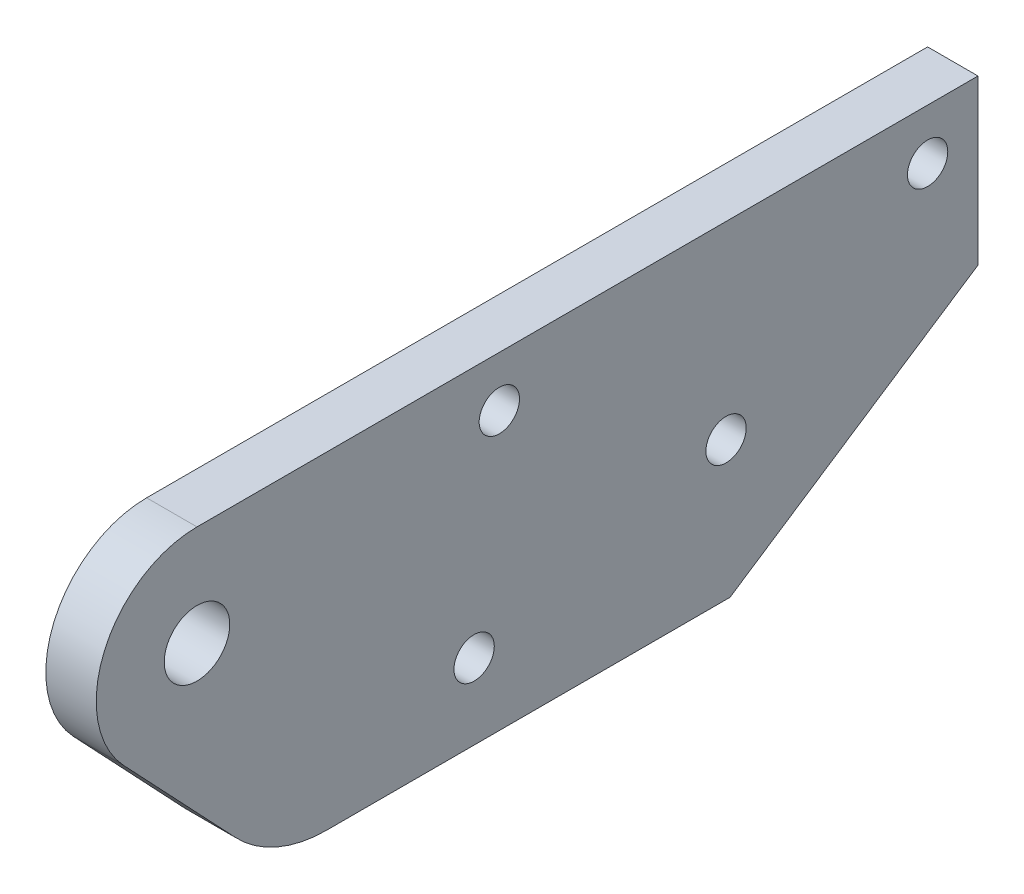
SolidWorks part; units mm, degrees
ref_plane "前视基准面" through (0, 0, 0) normal (0, 0, 1) x (1, 0, 0)
ref_plane "上视基准面" through (0, 0, 0) normal (0, 1, 0) x (1, 0, 0)
ref_plane "右视基准面" through (0, 0, 0) normal (1, 0, 0) x (0, 0, -1)
sketch "草图1" plane through (0, 0, 0) normal (1, 0, 0) x (0, 0, -1)
  line L0 (8.1049, 1.8788) -> (27.7954, 14.8788)
  line L1 (27.7954, 27.8788) -> (-34.2046, 27.8788)
  line L2 (27.7954, 27.8788) -> (27.7954, 14.8788)
  line L3 (8.1049, 1.8788) -> (-23.8951, 1.8788)
  line L10 (-31.1641, 5.0114) -> (-40.0198, 14.3849)
  circle A0 centre (23.7954, 23.8788) radius 1.6
  circle A1 centre (-10.2046, 23.8788) radius 1.6
  arc A2 (-34.2046, 27.8788) -> (-40.0198, 14.3849) centre (-34.2046, 19.8788) ccw
  circle A3 centre (7.7954, 12.8788) radius 1.6
  circle A4 centre (-12.2046, 7.8788) radius 1.6
  circle A5 centre (-34.2046, 19.8788) radius 2.6
  arc A6 (-23.8951, 1.8788) -> (-31.1641, 5.0114) centre (-23.8951, 11.8788) cw
  point P0 (-150, 0)
  point P1 (135, 0)
  point P9 (-344.9533, 138.7825)
  point P10 (187.1329, 101.1747)
  point P11 (165.9429, -19)
  point P12 (-156.9154, -19)
  dimension "D7" = 13
  dimension "D8" = 32
  dimension "D9" = 24
  dimension "D10" = 26
  dimension "D4" = 22
  dimension "D11" = 8
  dimension "D16" = 62
  dimension "D19" = 34
  dimension "D20" = 3.2
  dimension "D6" = 11
  dimension "D5" = 6
  dimension "D21" = 4
  dimension "D22" = 3.2
  dimension "D23" = 3.2
  dimension "D24" = 3.2
  dimension "D28" = 10
  dimension "D3" = 4
  dimension "D26" = 20
  dimension "D27" = 5.2
extrude "凸台-拉伸1" add sketch "草图1" along normal blind 4
